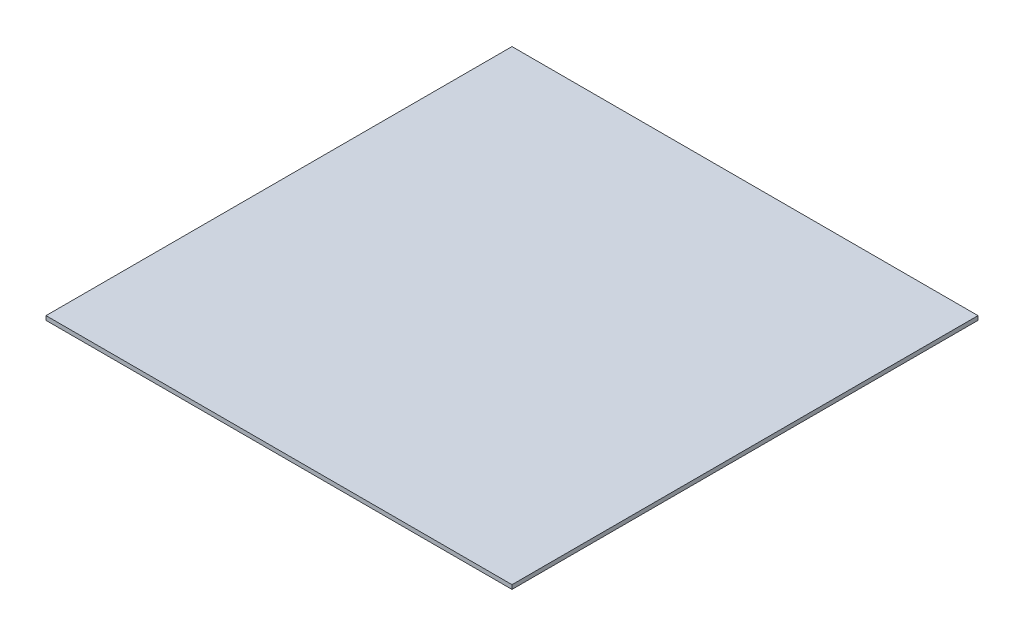
SolidWorks part; units mm, degrees
other "PCB"
ref_plane "Front Plane" through (0, 0, 0) normal (0, 0, 1) x (1, 0, 0)
ref_plane "Top Plane" through (0, 0, 0) normal (0, 1, 0) x (1, 0, 0)
ref_plane "Right Plane" through (0, 0, 0) normal (1, 0, 0) x (0, 0, -1)
sketch "Sketch1" plane through (0, 0, 0) normal (0, 1, 0) x (1, 0, 0)
  line L1 (-112.5, -112.5) -> (112.5, -112.5)
  line L2 (-112.5, -112.5) -> (-112.5, 112.5)
  line L3 (-112.5, 112.5) -> (112.5, 112.5)
  line L4 (112.5, -112.5) -> (112.5, 112.5)
  line L5 (-112.5, -112.5) -> (112.5, 112.5) construction
  line L6 (-112.5, 112.5) -> (112.5, -112.5) construction
  point P0 (0, 0)
  dimension "D1" = 225
extrude "Boss-Extrude1" add sketch "Sketch1" along normal blind 2
